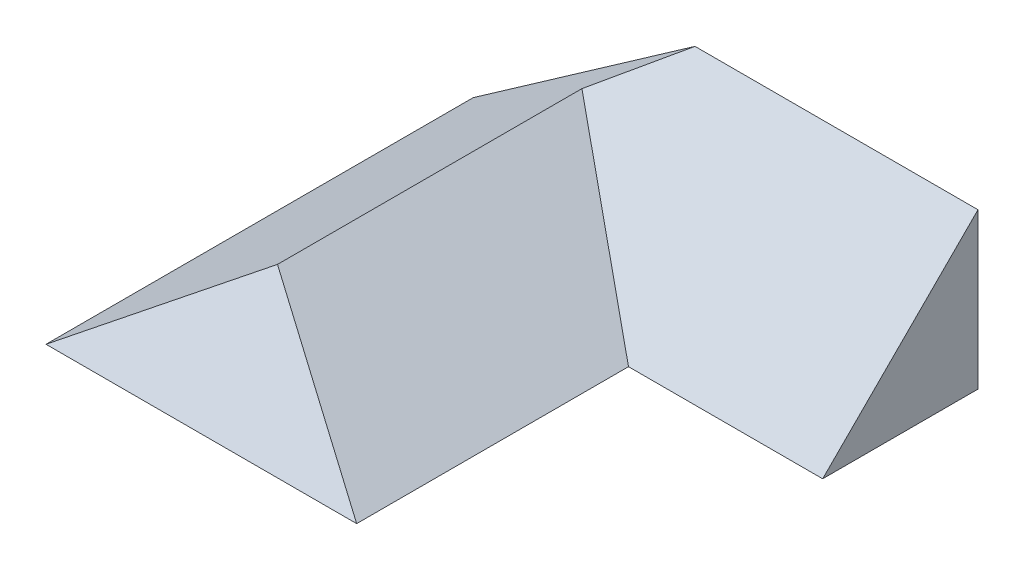
SolidWorks part; units mm, degrees
ref_plane "Front" through (0, 0, 0) normal (0, 0, 1) x (1, 0, 0)
ref_plane "Top" through (0, 0, 0) normal (0, 1, 0) x (1, 0, 0)
ref_plane "Right" through (0, 0, 0) normal (1, 0, 0) x (0, 0, -1)
sketch "Sketch1" plane through (0, 0, 0) normal (0, 0, 1) x (1, 0, 0)
  line L0 (0, 0) -> (80, 0)
  line L1 (80, 0) -> (40, 28.0083)
  line L2 (40, 0) -> (40, 28.0083) construction
  line L3 (0, 0) -> (40, 28.0083)
  dimension "D1" = 80
  dimension "D2" = 35
extrude "Extrude1" add sketch "Sketch1" against normal blind 110
sketch "Sketch2" plane through (0, 0, 0) normal (1, 0, 0) x (0, 0, -1)
  line L2 (0, 0) -> (19.6116, 28.0083)
  line L3 (19.6116, 28.0083) -> (0, 28.0083)
  line L4 (110, 28.0083) -> (0, 28.0083) construction
  line L5 (0, 28.0083) -> (0, 0)
extrude "Cut-Extrude1" cut sketch "Sketch2" along normal through all
ref_plane "Plane1" through (130, 0, 0) normal (1, 0, 0) x (0, 0, -1)
sketch "Sketch3" plane through (130, 0, 0) normal (1, 0, 0) x (0, 0, -1)
  line L0 (110, 0) -> (70, 0)
  line L1 (110, 0) -> (0, 0) construction
  line L2 (70, 0) -> (110, 40)
  line L3 (110, 0) -> (110, 40)
  dimension "D1" = 40
  dimension "D2" = 45
extrude "Extrude2" add sketch "Sketch3" against normal blind 90
sketch "Sketch4" plane through (0, 0, 0) normal (-0.5736, 0.8192, 0) x (-0.8192, -0.5736, 0)
  line L1 (0, -110) -> (-71.5602, -110)
  line L2 (0, -110) -> (0, -75.8073)
  line L3 (0, -75.8073) -> (-71.5602, -75.8073)
  line L4 (-71.5602, -110) -> (-71.5602, -75.8073)
extrude "Cut-Extrude2" cut sketch "Sketch4" along normal blind 10
ref_plane "AC Dihedral Angle Plane" through (60, 14.0042, -9.8058) normal (0.7601, -0.5323, 0.3727) x (0.3053, -0.2138, -0.928)
